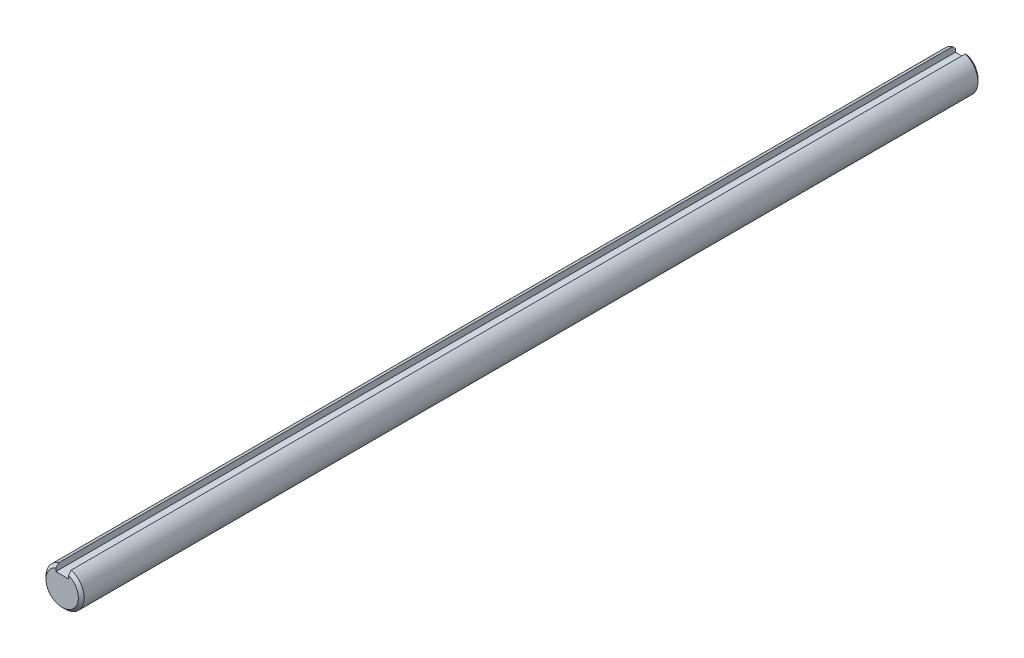
SolidWorks part; units mm, degrees
ref_plane "Front" through (0, 0, 0) normal (0, 0, 1) x (1, 0, 0)
ref_plane "Top" through (0, 0, 0) normal (0, 1, 0) x (1, 0, 0)
ref_plane "Right" through (0, 0, 0) normal (1, 0, 0) x (0, 0, -1)
sketch "Sketch1" plane through (0, 0, 0) normal (0, 0, 1) x (1, 0, 0)
  circle A0 centre (0, 0) radius 9
  dimension "dia" = 18
extrude "Extrude1" add sketch "Sketch1" along normal mid plane 425
sketch "Sketch2" plane through (0, 0, 0) normal (1, 0, 0) x (0, 0, -1)
  point P0 (-212.5, 9)
  point P1 (212.5, 9)
  point P2 (212.5, -9)
chamfer "Chamfer1" distance 1.35 angle 45 2 edges at (9, 0, -212.5) (9, 0, 212.5)
sketch "Sketch3" plane through (0, 0, 0) normal (0, 0, 1) x (1, 0, 0)
  line L1 (-3, 9) -> (3, 9)
  line L2 (-3, 9) -> (-3, 5.5)
  line L3 (-3, 5.5) -> (3, 5.5)
  line L4 (3, 9) -> (3, 5.5)
  dimension "key wd" = 6
  dimension "key dp" = 3.5
extrude "Extrude2" cut sketch "Sketch3" against normal through all and the other way through all
equation "\"D1@Chamfer1\" = \"dia@Sketch1\" * .075"
